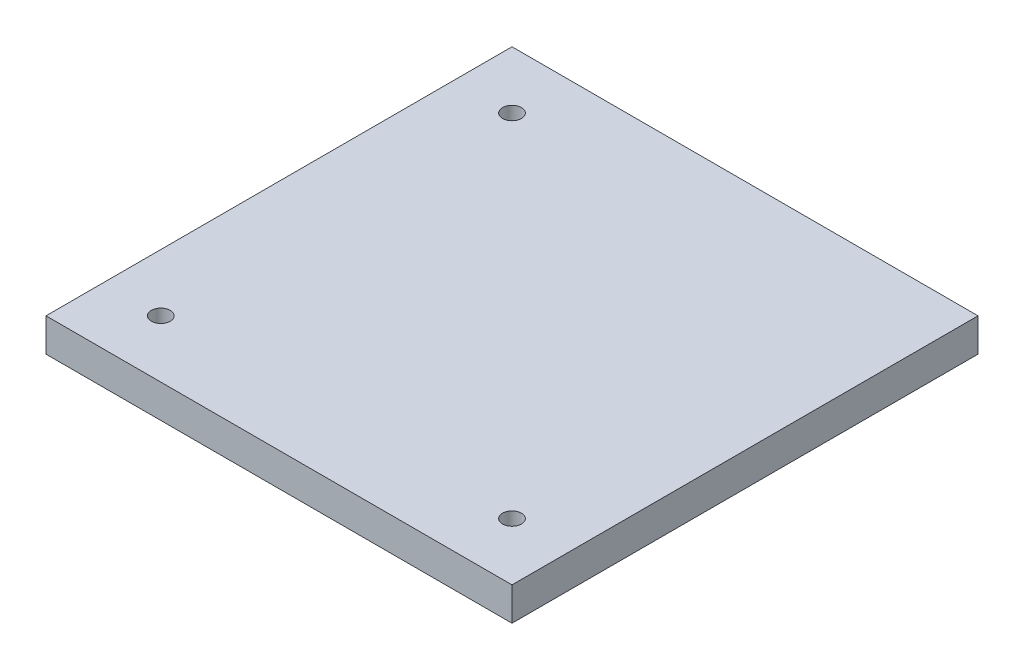
SolidWorks part; units mm, degrees
ref_plane "Front Plane" through (0, 0, 0) normal (0, 0, 1) x (1, 0, 0)
ref_plane "Top Plane" through (0, 0, 0) normal (0, 1, 0) x (1, 0, 0)
ref_plane "Right Plane" through (0, 0, 0) normal (1, 0, 0) x (0, 0, -1)
sketch "Sketch1" plane through (0, 0, 0) normal (0, 1, 0) x (1, 0, 0)
  line L1 (0, 0) -> (70.104, 0)
  line L2 (0, 0) -> (0, 70.104)
  line L3 (0, 70.104) -> (70.104, 70.104)
  line L4 (70.104, 0) -> (70.104, 70.104)
extrude "Boss-Extrude1" add sketch "Sketch1" along normal blind 5
sketch "Sketch2" plane through (0, 5, 0) normal (0, 1, 0) x (1, 0, 0)
  line L0 (35.052, 70.104) -> (35.052, 0) construction
  line L1 (70.104, 70.104) -> (0, 70.104) construction
  line L2 (0, 0) -> (70.104, 0) construction
  line L3 (0, 35.052) -> (70.104, 35.052) construction
  line L4 (0, 70.104) -> (0, 0) construction
  line L5 (70.104, 0) -> (70.104, 70.104) construction
  circle A0 centre (8.636, 8.636) radius 1.4224
  circle A1 centre (8.636, 61.468) radius 1.4224
  circle A2 centre (61.468, 8.636) radius 1.4224
extrude "Cut-Extrude1" cut sketch "Sketch2" against normal blind 6.35
